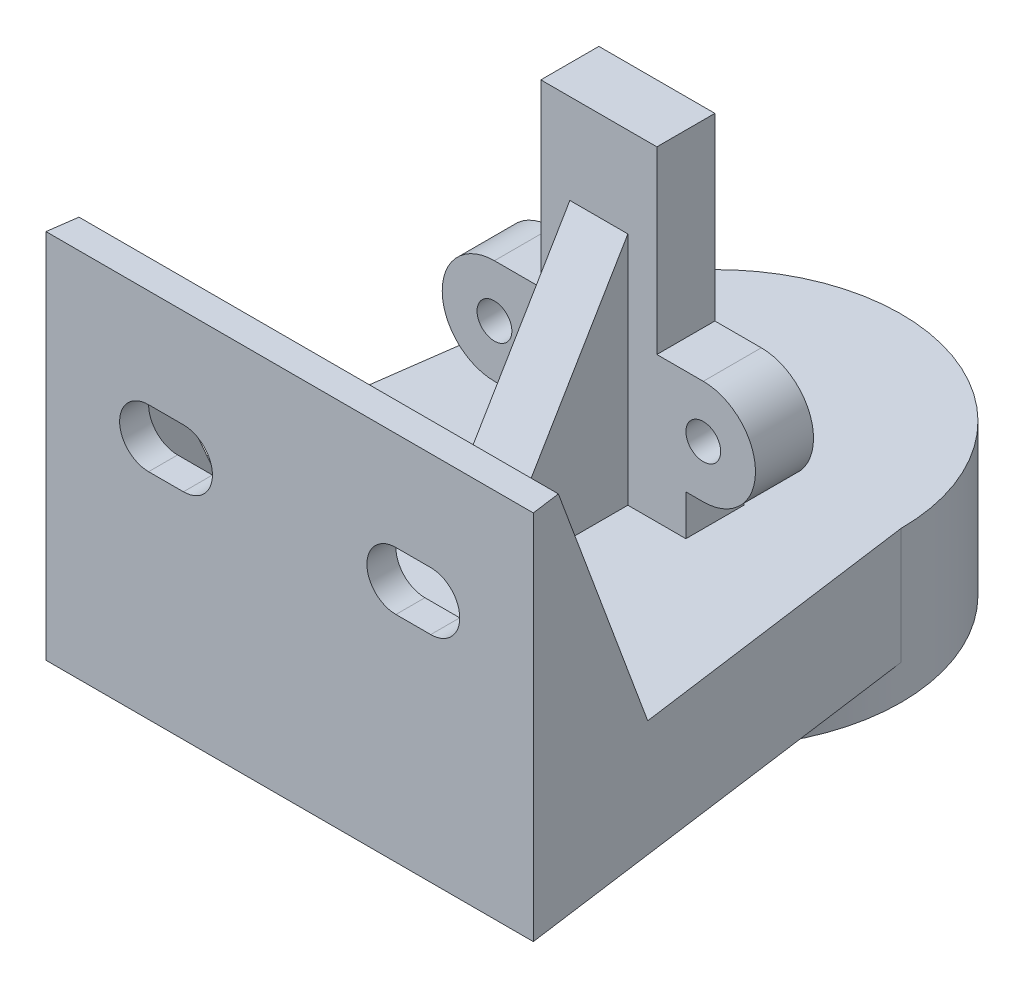
SolidWorks part; units mm, degrees
ref_plane "Front Plane" through (0, 0, 0) normal (0, 0, 1) x (1, 0, 0)
ref_plane "Top Plane" through (0, 0, 0) normal (0, 1, 0) x (1, 0, 0)
ref_plane "Right Plane" through (0, 0, 0) normal (1, 0, 0) x (0, 0, -1)
sketch "Sketch1" plane through (0, 0, 0) normal (0, 1, 0) x (1, 0, 0)
  circle A0 centre (0, 0) radius 16
  dimension "D1" = 32
extrude "Boss-Extrude1" add sketch "Sketch1" along normal blind 13
sketch "Sketch2" plane through (0, 0, 0) normal (0, -1, 0) x (1, 0, 0)
  circle A0 centre (0, 0) radius 12.55
  dimension "D1" = 25.1
extrude "Cut-Extrude1" cut sketch "Sketch2" against normal blind 8
sketch "Sketch3" plane through (0, 13, 0) normal (0, 1, 0) x (1, 0, 0)
  circle A0 centre (0, 0) radius 4.05
  dimension "D1" = 8.1
extrude "Cut-Extrude2" cut sketch "Sketch3" against normal up to surface (5 mm away) up to face at (0, 8, -12.55)
sketch "Sketch4" plane through (0, 13, 0) normal (0, 1, 0) x (1, 0, 0)
  line L1 (7.5, -10.05) -> (7.5, -5.05)
  line L2 (7.5, -10.05) -> (-7.5, -10.05)
  line L3 (7.5, -5.05) -> (-7.5, -5.05)
  line L4 (-7.5, -10.05) -> (-7.5, -5.05)
  line L5 (7.5, -10.05) -> (-7.5, -5.05) construction
  line L6 (7.5, -5.05) -> (-7.5, -10.05) construction
  point P0 (0, 0)
  point P1 (0, -5.05)
  point P4 (0, 0)
  point P5 (0, -7.55)
  dimension "D1" = 15
  dimension "D2" = 5
  dimension "D3" = 5.05
extrude "Boss-Extrude2" add sketch "Sketch4" along normal blind 28
sketch "Sketch6" plane through (0, 0, 5.05) normal (0, 0, -1) x (-1, 0, 0)
  line L0 (7.5, 16.5) -> (9, 16.5)
  line L1 (7.5, 41) -> (7.5, 13) construction
  line L2 (9, 25.5) -> (7.5, 25.5)
  line L3 (7.5, 16.5) -> (7.5, 25.5)
  line L4 (-7.5, 16.5) -> (-9, 16.5)
  line L5 (-7.5, 41) -> (-7.5, 13) construction
  line L6 (-9, 25.5) -> (-7.5, 25.5)
  line L7 (-7.5, 16.5) -> (-7.5, 25.5)
  arc A0 (9, 16.5) -> (9, 25.5) centre (9, 21) ccw
  arc A2 (-9, 25.5) -> (-9, 16.5) centre (-9, 21) ccw
  dimension "D3" = 9
  dimension "D1" = 3.5
  dimension "D2" = 1.5
extrude "Boss-Extrude5" add sketch "Sketch6" against normal up to surface (5 mm away) up to face at (0, 27, 10.05)
sketch "Sketch7" plane through (0, 0, 5.05) normal (0, 0, -1) x (-1, 0, 0)
  line L0 (7.5, 25.5) -> (5, 25.5)
  line L1 (5, 25.5) -> (5, 41)
  line L2 (-7.5, 41) -> (7.5, 41) construction
  line L3 (5, 41) -> (7.5, 41)
  line L4 (7.5, 41) -> (7.5, 25.5)
  line L5 (-7.5, 25.5) -> (-5, 25.5)
  line L6 (-5, 25.5) -> (-5, 41)
  line L7 (-5, 41) -> (-7.5, 41)
  line L8 (-7.5, 41) -> (-7.5, 25.5)
  circle A0 centre (-9, 21) radius 1.5
  circle A1 centre (9, 21) radius 1.5
  dimension "D2" = 3
  dimension "D1" = 2.5
extrude "Cut-Extrude3" cut sketch "Sketch7" against normal up to surface (5 mm away) up to face at (0, 23, 10.05)
sketch "Sketch8" plane through (0, 13, 0) normal (0, 1, 0) x (1, 0, 0)
  line L1 (-21, -36.7) -> (21, -36.7)
  line L3 (-15.9963, -0.3427) -> (-21, -36.7)
  line L4 (16, 0) -> (21, -36.7)
  circle A0 centre (0, 0) radius 16 construction
  circle A2 centre (0, 0) radius 16
  arc A3 (-15.9963, -0.3427) -> (16, 0) centre (0, 0) ccw
  point P4 (0, -36.7)
  dimension "D1" = 36.7
  dimension "D3" = 42
  dimension "D2" = 0
extrude "Boss-Extrude6" add sketch "Sketch8" against normal blind 10
sketch "Sketch9" plane through (0, 13, 0) normal (0, 1, 0) x (1, 0, 0)
  line L5 (-21, -36.7) -> (21, -36.7)
  line L6 (21, -36.7) -> (20.6594, -34.2)
  line L7 (21, -36.7) -> (16, 0) construction
  line L8 (20.6594, -34.2) -> (-20.6559, -34.2)
  line L9 (-15.9963, -0.3427) -> (-21, -36.7) construction
  line L10 (-20.6559, -34.2) -> (-21, -36.7)
  dimension "D1" = 2.5
extrude "Boss-Extrude7" add sketch "Sketch9" along normal blind 22
sketch "Sketch11" plane through (0, 0, 34.2) normal (0, 0, -1) x (-1, 0, 0)
  line L0 (12.1559, 24) -> (9.1559, 24) construction
  line L1 (12.1559, 21.5) -> (9.1559, 21.5)
  line L2 (12.1559, 26.5) -> (9.1559, 26.5)
  line L3 (-20.6594, 13) -> (20.6559, 13) construction
  line L4 (20.6559, 35) -> (20.6559, 13) construction
  line L5 (-9.1594, 24) -> (-12.1594, 24) construction
  line L6 (-9.1594, 21.5) -> (-12.1594, 21.5)
  line L7 (-9.1594, 26.5) -> (-12.1594, 26.5)
  line L8 (-20.6594, 35) -> (-20.6594, 13) construction
  arc A0 (12.1559, 21.5) -> (12.1559, 26.5) centre (12.1559, 24) ccw
  arc A1 (9.1559, 26.5) -> (9.1559, 21.5) centre (9.1559, 24) ccw
  arc A2 (-9.1594, 21.5) -> (-9.1594, 26.5) centre (-9.1594, 24) ccw
  arc A3 (-12.1594, 26.5) -> (-12.1594, 21.5) centre (-12.1594, 24) ccw
  point P2 (10.6559, 24)
  point P9 (14.6559, 24)
  point P12 (6.6559, 24)
  point P15 (-10.6594, 24)
  point P20 (-6.6594, 24)
  point P21 (-14.6594, 24)
  dimension "D1" = 11
  dimension "D2" = 6
  dimension "D3" = 5
  dimension "D4" = 8
  dimension "D5" = 6
  dimension "D6" = 11
extrude "Cut-Extrude5" cut sketch "Sketch11" against normal up to surface (2.5 mm away) up to face at (0, 19, 36.7)
sketch "Sketch12" plane through (-15.6527, 0, -2.1542) normal (-0.9907, 0, -0.1363) x (-0.1363, 0, 0.9907)
  line L0 (36.6969, 13) -> (27.6969, 13)
  line L1 (2.5204, 13) -> (36.6969, 13) construction
  line L2 (27.6969, 13) -> (36.6969, 35)
  line L3 (36.6969, 35) -> (36.6969, 13) construction
  line L4 (36.6969, 35) -> (39.2204, 35) construction
  line L5 (36.6969, 35) -> (36.6969, 13)
  dimension "D1" = 9
extrude "Boss-Extrude8" add sketch "Sketch12" against normal blind 2 separate body
sketch "Sketch13" plane through (15.7084, 0, -2.1401) normal (0.9908, 0, -0.135) x (-0.135, 0, -0.9908)
  line L0 (-36.6758, 13) -> (-27.6758, 13)
  line L1 (-36.6758, 13) -> (-2.1599, 13) construction
  line L2 (-27.6758, 13) -> (-36.6758, 35)
  line L3 (-36.6758, 35) -> (-36.6758, 13)
  dimension "D1" = 9
extrude "Boss-Extrude9" add sketch "Sketch13" against normal blind 2
sketch "Sketch14" plane through (0, 0, 10.05) normal (0, 0, 1) x (1, 0, 0)
  line L5 (2.5, 13) -> (-2.5, 13)
  line L7 (-2.5, 33.25) -> (2.5, 33.25)
  line L8 (-2.5, 33.25) -> (-2.5, 13)
  line L9 (2.5, 33.25) -> (2.5, 13)
  point P13 (0, 33.25)
  dimension "D1" = 5
extrude "Boss-Extrude10" add sketch "Sketch14" along normal blind 12
sketch "Sketch15" plane through (-2.5, 0, 0) normal (-1, 0, 0) x (0, 0, 1)
  line L0 (10.05, 33.25) -> (22.05, 13)
  line L1 (22.05, 13) -> (22.05, 33.25)
  line L2 (22.05, 33.25) -> (10.05, 33.25)
extrude "Cut-Extrude6" cut sketch "Sketch15" against normal up to surface (5 mm away) up to face at (2.5, 23.125, 16.05)
